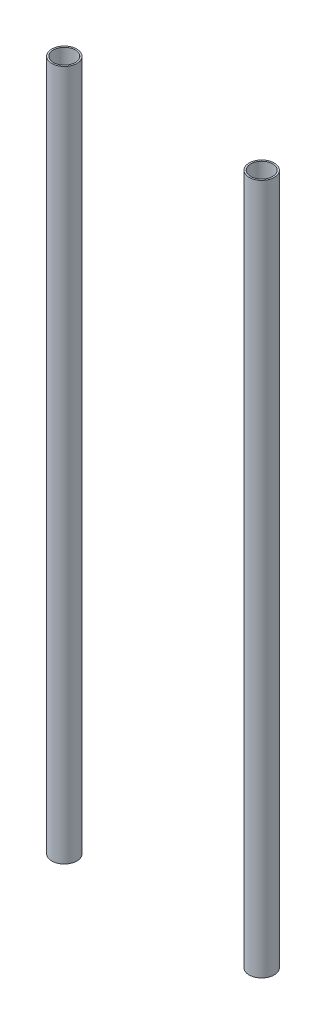
SolidWorks part; units mm, degrees
ref_plane "Front" through (0, 0, 0) normal (0, 0, 1) x (1, 0, 0)
ref_plane "Top" through (0, 0, 0) normal (0, 1, 0) x (1, 0, 0)
ref_plane "Right" through (0, 0, 0) normal (1, 0, 0) x (0, 0, -1)
sketch "Sketch1" plane through (0, 0, 0) normal (0, 1, 0) x (1, 0, 0)
  line L0 (100, 0) -> (-100, 0) construction
  circle A0 centre (-100, 0) radius 11.1
  circle A1 centre (-100, 0) radius 12.7
  circle A2 centre (100, 0) radius 12.7
  circle A3 centre (100, 0) radius 11.1
  point P11 (0, 0)
  dimension "D1" = 1.6
  dimension "D2" = 25.4
  dimension "D3" = 25.4
  dimension "D4" = 1.6
extrude "Boss-Extrude1" add sketch "Sketch1" along normal blind 700
